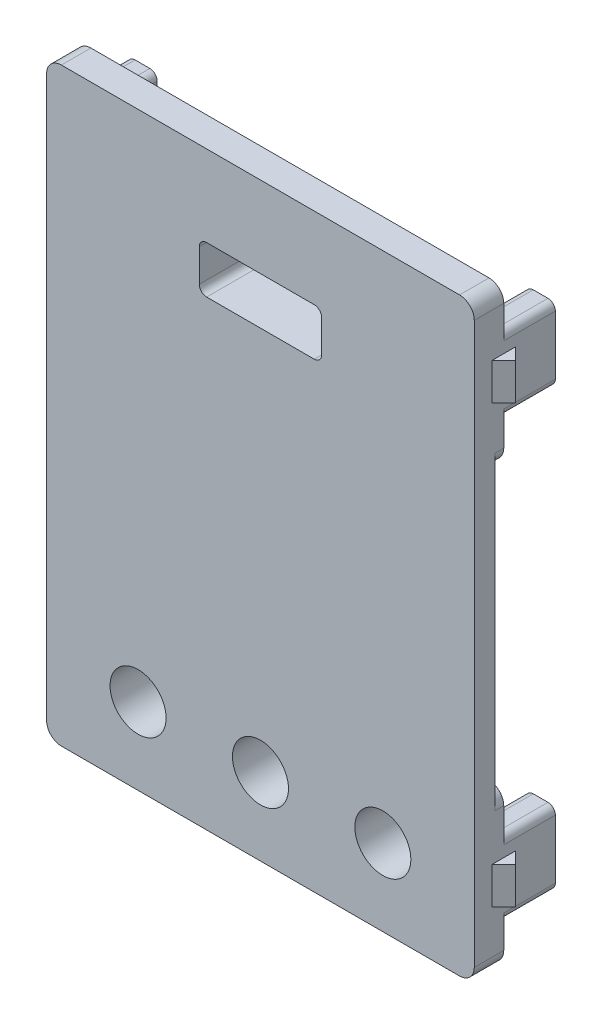
SolidWorks part; units mm, degrees
ref_plane "前视基准面" through (0, 0, 0) normal (0, 0, 1) x (1, 0, 0)
ref_plane "上视基准面" through (0, 0, 0) normal (0, 1, 0) x (1, 0, 0)
ref_plane "右视基准面" through (0, 0, 0) normal (1, 0, 0) x (0, 0, -1)
sketch "草图1" plane through (0, 0, 0) normal (0, 0, 1) x (1, 0, 0)
  line L1 (0, 0) -> (29, 0)
  line L2 (0, 0) -> (0, 40)
  line L3 (0, 40) -> (29, 40)
  line L4 (29, 0) -> (29, 40)
  dimension "D1" = 29
  dimension "D2" = 40
extrude "凸台-拉伸1" add sketch "草图1" along normal blind 2
sketch "草图2" plane through (0, 0, 0) normal (0, 0, -1) x (-1, 0, 0)
  line L0 (-14.5, 40) -> (-14.5, 0) construction
  line L1 (-29, 40) -> (0, 40) construction
  line L2 (0, 0) -> (-29, 0) construction
  line L3 (-29, 20) -> (0, 20) construction
  line L4 (-29, 0) -> (-29, 40) construction
  line L5 (0, 40) -> (0, 0) construction
  line L6 (-2, 37.3) -> (-2, 32.3)
  line L7 (-29, 37.3) -> (-27, 37.3)
  line L8 (-29, 37.3) -> (-29, 32.3)
  line L9 (-29, 32.3) -> (-27, 32.3)
  line L10 (-27, 37.3) -> (-27, 32.3)
  line L11 (0, 32.3) -> (-2, 32.3)
  line L12 (0, 37.3) -> (0, 32.3)
  line L13 (0, 37.3) -> (-2, 37.3)
  line L14 (0, 2.7) -> (-2, 2.7)
  line L15 (0, 2.7) -> (0, 7.7)
  line L16 (0, 7.7) -> (-2, 7.7)
  line L17 (-27, 2.7) -> (-27, 7.7)
  line L18 (-29, 7.7) -> (-27, 7.7)
  line L19 (-29, 2.7) -> (-29, 7.7)
  line L20 (-29, 2.7) -> (-27, 2.7)
  line L21 (-2, 2.7) -> (-2, 7.7)
  dimension "D1" = 2
  dimension "D2" = 24.6
  dimension "D3" = 5
  dimension "D4" = 7.7
extrude "凸台-拉伸2" add sketch "草图2" along normal blind 3.5
sketch "草图3" plane through (0, 0, 2) normal (0, 0, 1) x (1, 0, 0)
  line L0 (14.5, 40) -> (14.5, 0) construction
  line L1 (29, 40) -> (0, 40) construction
  line L2 (0, 0) -> (29, 0) construction
  line L4 (10.35, 31.3) -> (18.65, 31.3)
  line L5 (10.35, 31.3) -> (10.35, 34.5)
  line L6 (10.35, 34.5) -> (18.65, 34.5)
  line L7 (18.65, 31.3) -> (18.65, 34.5)
  line L8 (10.35, 31.3) -> (18.65, 34.5) construction
  line L9 (10.35, 34.5) -> (18.65, 31.3) construction
  point P6 (14.5, 32.9)
  dimension "D1" = 8.3
  dimension "D2" = 3.2
  dimension "D3" = 5.5
extrude "切除-拉伸1" cut sketch "草图3" against normal through all
sketch "草图4" plane through (0, 0, 2) normal (0, 0, 1) x (1, 0, 0)
  line L0 (14.5, 40) -> (14.5, 0) construction
  line L1 (29, 40) -> (0, 40) construction
  line L2 (0, 0) -> (29, 0) construction
  line L3 (0, 5.2) -> (29, 5.2) construction
  line L4 (0, 40) -> (0, 0) construction
  line L5 (29, 0) -> (29, 40) construction
  circle A0 centre (14.5, 5.2) radius 1.9
  circle A1 centre (6.2, 5.2) radius 1.9
  circle A2 centre (22.8, 5.2) radius 1.9
  dimension "D2" = 3.8
  dimension "D1" = 5.2
  dimension "D3" = 8.3
  dimension "D4" = 8.3
extrude "切除-拉伸2" cut sketch "草图4" against normal through all
sketch "草图5" plane through (0, 0, 0) normal (0, 0, -1) x (-1, 0, 0)
  line L0 (-10.35, 31.3) -> (-10.35, 34.5) construction
  line L1 (-10.35, 34.5) -> (-18.65, 34.5) construction
  line L2 (-18.65, 34.5) -> (-18.65, 31.3) construction
  line L3 (-18.65, 31.3) -> (-10.35, 31.3) construction
  line L4 (-10.35, 31.3) -> (-10.35, 34.5)
  line L5 (-10.35, 34.5) -> (-18.65, 34.5)
  line L6 (-18.65, 34.5) -> (-18.65, 31.3)
  line L7 (-18.65, 31.3) -> (-10.35, 31.3)
  line L8 (-9.15, 30.1) -> (-9.15, 35.7)
  line L9 (-9.15, 35.7) -> (-19.85, 35.7)
  line L10 (-19.85, 35.7) -> (-19.85, 30.1)
  line L11 (-19.85, 30.1) -> (-9.15, 30.1)
  dimension "D1" = 1.2
extrude "凸台-拉伸3" add sketch "草图5" along normal blind 2
sketch "草图6" plane through (0, 0, 0) normal (0, 0, -1) x (-1, 0, 0)
  circle A0 centre (-6.2, 5.2) radius 1.9 construction
  circle A1 centre (-14.5, 5.2) radius 1.9 construction
  circle A2 centre (-22.8, 5.2) radius 1.9 construction
  circle A3 centre (-6.2, 5.2) radius 1.9
  circle A4 centre (-14.5, 5.2) radius 1.9
  circle A5 centre (-22.8, 5.2) radius 1.9
  circle A6 centre (-22.8, 5.2) radius 3.1
  circle A7 centre (-14.5, 5.2) radius 3.1
  circle A8 centre (-6.2, 5.2) radius 3.1
  dimension "D1" = 1.2
  dimension "D2" = 1.2
  dimension "D3" = 1.2
extrude "凸台-拉伸4" add sketch "草图6" along normal blind 1
ref_plane "基准面1" through (0, 34.8, 0) normal (0, -1, 0) x (-1, 0, 0)
sketch "草图10" plane through (0, 34.8, 0) normal (0, -1, 0) x (-1, 0, 0)
  line L0 (-29, 0.8) -> (-29.8, 0)
  line L1 (-29, 3.5) -> (-29, 0) construction
  line L2 (-29.8, 0) -> (-29, -0.8)
  line L4 (-29, -0.8) -> (-29, 0.8)
  line L5 (-14.5, -2) -> (-14.5, 2) construction
  line L6 (0, -2) -> (-29, -2) construction
  line L7 (-19.85, 2) -> (-9.15, 2) construction
  line L11 (-29.8, 0) -> (0.8, 0) construction
  line L12 (-29, -2) -> (-29, 0) construction
  line L13 (0, -0.8) -> (0, 0.8)
  line L14 (0.8, 0) -> (0, -0.8)
  line L15 (0, 0.8) -> (0.8, 0)
  dimension "D1" = 2
  dimension "D2" = 0.8
extrude "凸台-拉伸5" add sketch "草图10" along normal mid plane 2.5
ref_plane "基准面2" through (0, 20, 0) normal (0, -1, 0) x (-1, 0, 0)
mirror "镜向1" about plane through (0, 20, 0) normal (0, -1, 0) of "凸台-拉伸5"
sketch "草图8" plane through (0, 0, -3.5) normal (0, 0, -1) x (-1, 0, 0)
  line L0 (-29, 37.3) -> (-29, 32.3) construction
  line L1 (0, 32.3) -> (0, 37.3) construction
  line L2 (-29, 7.7) -> (-29, 2.7) construction
  line L3 (0, 2.7) -> (0, 7.7) construction
  line L4 (-29, 35.2) -> (-29, 34.4)
  line L5 (0, 35.2) -> (0, 34.4)
  line L6 (-29, 5.6) -> (-29, 4.8)
  line L7 (0, 5.6) -> (0, 4.8)
  arc A0 (-29, 34.4) -> (-29, 35.2) centre (-29, 34.8) cw
  arc A1 (0, 34.4) -> (0, 35.2) centre (0, 34.8) ccw
  arc A2 (-29, 4.8) -> (-29, 5.6) centre (-29, 5.2) cw
  arc A3 (0, 4.8) -> (0, 5.6) centre (0, 5.2) ccw
  dimension "D1" = 0.4
fillet "圆角1" radius 0.5 16 edges at (29, 32.3, -1.75) (27, 32.3, -1.75) (29, 2.7, -1.75) (27, 2.7, -1.75) (2, 2.7, -1.75) (0, 2.7, -1.75) (2, 32.3, -1.75) (0, 32.3, -1.75) (29, 37.3, -1.75) (27, 37.3, -1.75) (29, 7.7, -1.75) (27, 7.7, -1.75) (2, 7.7, -1.75) (0, 7.7, -1.75) (2, 37.3, -1.75) (0, 37.3, -1.75)
fillet "圆角2" radius 0.5 4 edges at (18.65, 31.3, 0) (18.65, 34.5, 0) (10.35, 31.3, 0) (10.35, 34.5, 0)
chamfer "倒角1" distance 0.2 angle 45 3 edges at (4.3, 5.2, -1) (12.6, 5.2, -1) (20.9, 5.2, -1)
chamfer "倒角2" distance 0.5 angle 45 8 edges at (14.5, 31.3, -2) (10.4964, 31.4464, -2) (18.5036, 31.4464, -2) (10.35, 32.9, -2) (18.65, 32.9, -2) (10.4964, 34.3536, -2) (18.5036, 34.3536, -2) (14.5, 34.5, -2)
fillet "圆角3" radius 1 4 edges at (29, 0, 1) (0, 0, 1) (0, 40, 1) (29, 40, 1)
fillet "圆角4" radius 1 4 edges at (9.15, 30.1, -1) (19.85, 30.1, -1) (9.15, 35.7, -1) (19.85, 35.7, -1)
sketch "草图9" plane through (0, 0, 0) normal (0, 0, -1) x (-1, 0, 0)
  line L0 (-29, 20) -> (0, 20) construction
  line L1 (-29, 7.2) -> (-29, 32.8) construction
  line L2 (0, 32.8) -> (0, 7.2) construction
  line L4 (-29, 10.5) -> (0, 10.5)
  line L5 (-29, 10.5) -> (-29, 29.5)
  line L6 (-29, 29.5) -> (0, 29.5)
  line L7 (0, 10.5) -> (0, 29.5)
  point P10 (-29, 20)
  dimension "D1" = 19
extrude "切除-拉伸3" cut sketch "草图9" against normal blind 0.6
fillet "圆角5" radius 1 4 edges at (0, 29.5, 0.3) (29, 29.5, 0.3) (0, 10.5, 0.3) (29, 10.5, 0.3)
